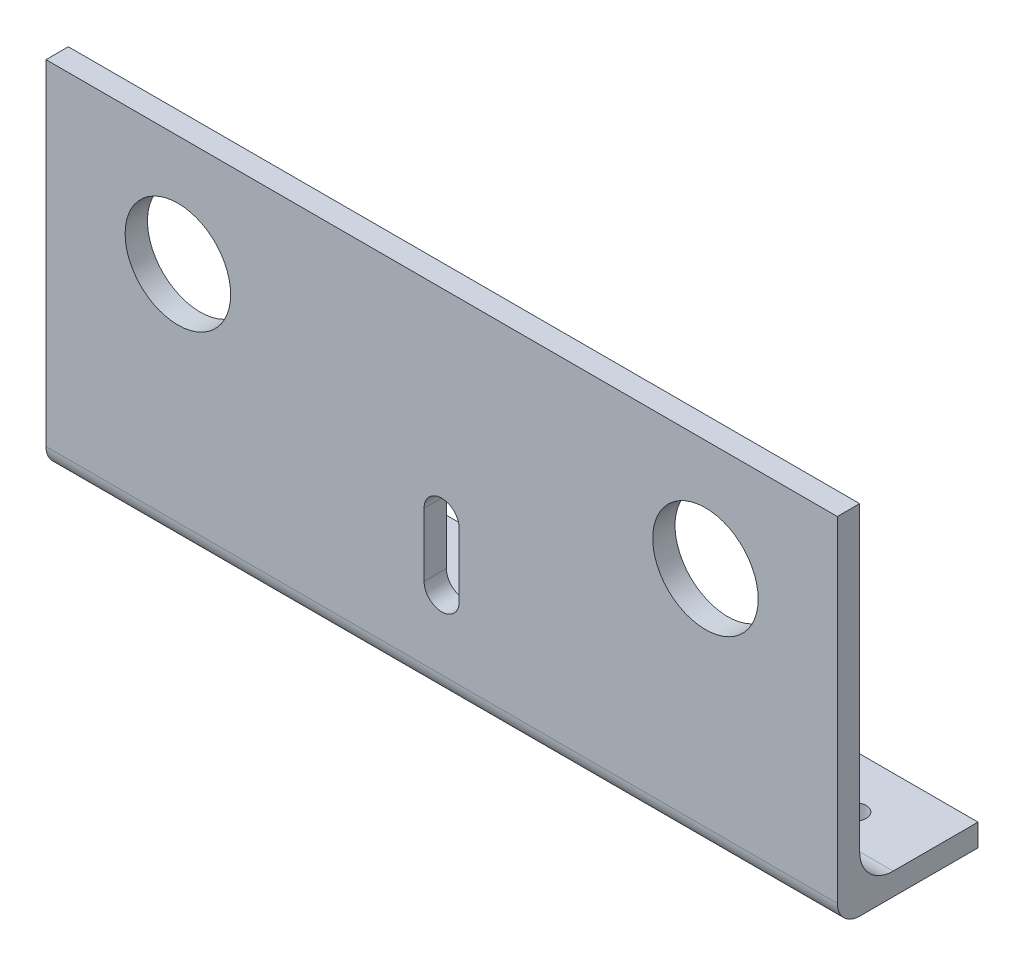
SolidWorks part; units mm, degrees
ref_plane "Front" through (0, 0, 0) normal (0, 0, 1) x (1, 0, 0)
ref_plane "Top" through (0, 0, 0) normal (0, 1, 0) x (1, 0, 0)
ref_plane "Right" through (0, 0, 0) normal (1, 0, 0) x (0, 0, -1)
sketch "Sketch1" plane through (0, 0, 0) normal (1, 0, 0) x (0, 0, -1)
  line L0 (0, 0) -> (0, 101.6)
  line L1 (0, 101.6) -> (6.35, 101.6)
  line L2 (6.35, 101.6) -> (6.35, 15.875)
  line L3 (15.875, 6.35) -> (40, 6.35)
  line L4 (40, 6.35) -> (40, 0)
  line L5 (40, 0) -> (0, 0)
  arc A0 (6.35, 15.875) -> (15.875, 6.35) centre (15.875, 15.875) ccw
  dimension "D3" = 9.525
  dimension "D1" = 40
  dimension "D2" = 6.35
  dimension "D4" = 85.725
  dimension "D5" = 101.6
extrude "Boss-Extrude1" add sketch "Sketch1" along normal blind 225
fillet "Fillet1" radius 6.35 1 edges at (112.5, 0, 0)
sketch "Sketch2" plane through (0, 0, 0) normal (0, 0, -1) x (-1, 0, 0)
  line L0 (-37.5, 0) -> (-37.5, 70) construction
  line L1 (-112.5, 15.875) -> (-112.5, 86.0363) construction
  line L2 (-225, 0) -> (0, 0) construction
  line L3 (-187.5, 0) -> (-187.5, 70) construction
  line L4 (0, 15.875) -> (0, 101.6)
  line L5 (0, 101.6) -> (-225, 101.6)
  line L6 (-225, 101.6) -> (-225, 15.875)
  line L7 (-225, 15.875) -> (0, 15.875)
  line L8 (0, 15.875) -> (0, 101.6) construction
  line L9 (0, 101.6) -> (-225, 101.6) construction
  line L10 (-225, 101.6) -> (-225, 15.875) construction
  line L11 (-225, 15.875) -> (0, 15.875) construction
  circle A1 centre (-37.5, 70) radius 15
  circle A2 centre (-187.5, 70) radius 15
  dimension "D2" = 37.5
  dimension "D4" = 30
  dimension "D3" = 70
  dimension "D1" = 0
extrude "Cut-Extrude1" cut sketch "Sketch2" along normal blind 75
sketch "Sketch5" plane through (0, 0, -6.35) normal (0, 0, -1) x (-1, 0, 0)
  line L0 (-112.5, 15.875) -> (-112.5, 35.875) construction
  line L1 (-225, 15.875) -> (0, 15.875) construction
  line L2 (-112.5, 44.875) -> (-112.5, 26.875) construction
  line L3 (-107.5, 44.875) -> (-107.5, 26.875)
  line L4 (-117.5, 44.875) -> (-117.5, 26.875)
  arc A0 (-107.5, 44.875) -> (-117.5, 44.875) centre (-112.5, 44.875) ccw
  arc A1 (-117.5, 26.875) -> (-107.5, 26.875) centre (-112.5, 26.875) ccw
  point P6 (-112.5, 35.875)
  point P11 (-112.5, 21.875)
  dimension "D1" = 10
  dimension "D2" = 18
  dimension "D3" = 6
extrude "Cut-Extrude2" cut sketch "Sketch5" against normal blind 10
sketch "Sketch3" plane through (0, 0, 0) normal (0, -1, 0) x (1, 0, 0)
  line L0 (20, -25) -> (70, -25) construction
  line L1 (112.5, -40) -> (112.5, -33.8713) construction
  line L2 (45, -25) -> (45, -40) construction
  line L4 (225, -40) -> (0, -40) construction
  line L5 (0, -6.35) -> (0, -40) construction
  line L6 (205, -25) -> (155, -25) construction
  line L7 (180, -25) -> (180, -40) construction
  point P7 (45, -25)
  dimension "D1" = 15
  dimension "D2" = 50
  dimension "D3" = 45
hole_wizard "M6 Clearance Hole1" positions "3DSketch1" profile "Sketch4" hole size "M6" standard "ANSI Metric" end condition through all
sketch3d "3DSketch1"
  point P0 (20, 0, -25)
  point P3 (70, 0, -25)
  point P6 (155, 0, -25)
  point P9 (205, 0, -25)
sketch "Sketch4" plane through (20, 0, -25) normal (1, 0, 0) x (0, 0, -1)
  line L0 (0, 0) -> (0, 101.6)
  line L1 (0, 101.6) -> (3.2, 101.6)
  line L2 (3.2, 101.6) -> (3.2, 0)
  line L5 (3.2, 0) -> (0, 0)
  line L11 (0, -6.35) -> (0, 107.95) construction
  dimension "Thru Hole Dia." = 6.4
  dimension "Thru Hole Depth" = 101.6
